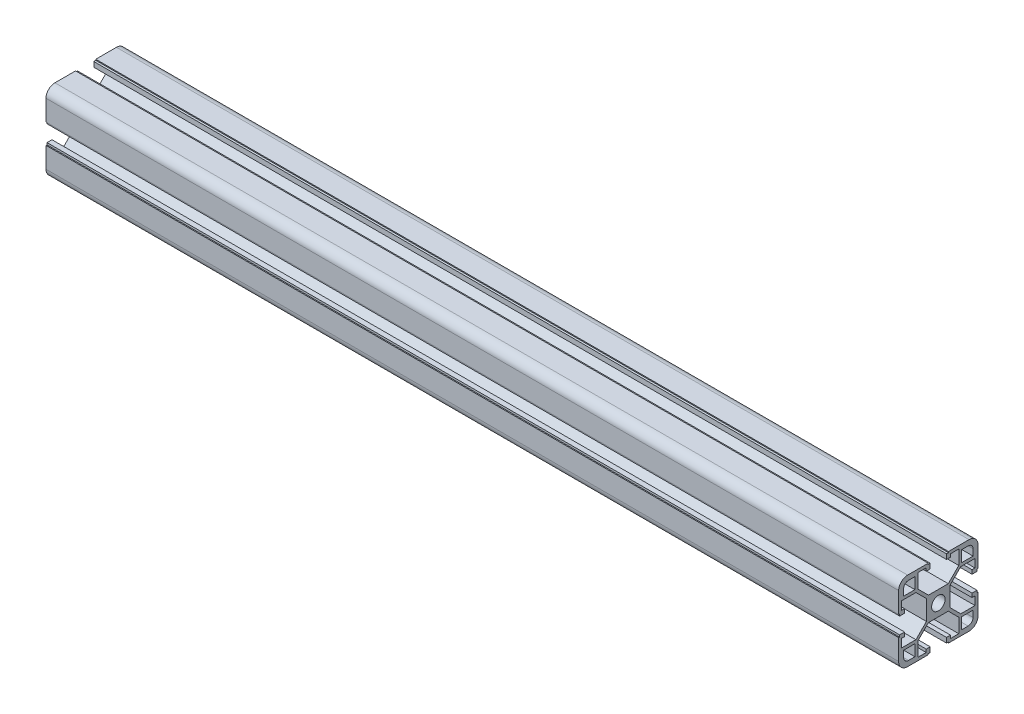
SolidWorks part; units mm, degrees
ref_plane "前视基准面" through (0, 0, 0) normal (0, 0, 1) x (1, 0, 0)
ref_plane "上视基准面" through (0, 0, 0) normal (0, 1, 0) x (1, 0, 0)
ref_plane "右视基准面" through (0, 0, 0) normal (1, 0, 0) x (0, 0, -1)
sketch "草图1" plane through (0, 0, 0) normal (0, 1, 0) x (1, 0, 0)
  line L0 (-165, 0) -> (265, 0)
  line L1 (0, 101.9544) -> (0, -23.3477) construction
  dimension "D1" = 430
  dimension "D2" = 165
other "铝型材 40 X 40L X R4.5(1)"
ref_plane "基准面1" through (-165, 0, 0) normal (1, 0, 0) x (0, 0, -1)
sketch "Sketch1" plane through (-165, 0, 0) normal (1, 0, 0) x (0, 0, -1)
  line L0 (-5.1, 20) -> (-5.1, 19.5)
  line L1 (-5.1, 19.5) -> (-4.1, 19.5)
  line L2 (-4.1, 19.5) -> (-4.1, 17)
  line L3 (-6.1, 18.5) -> (-10.3, 18.5)
  line L4 (-15.5, -20) -> (-5.1, -20)
  line L5 (-20, -15.5) -> (-20, -5.1)
  line L6 (15.5, 20) -> (5.1, 20)
  line L7 (20, 15.5) -> (20, 5.1)
  line L8 (0, 14.8756) -> (0, 0) construction
  line L9 (0, 0) -> (14.1675, 0) construction
  line L10 (-10.3, 18.5) -> (-10.3, 11.3)
  line L11 (-10.3, 11.3) -> (-5, 6)
  line L12 (-5, 6) -> (5, 6)
  line L13 (10.3, 11.3) -> (5, 6)
  line L14 (10.3, 18.5) -> (10.3, 11.3)
  line L15 (6.1, 18.5) -> (10.3, 18.5)
  line L16 (4.1, 19.5) -> (4.1, 17)
  line L17 (5.1, 19.5) -> (4.1, 19.5)
  line L18 (5.1, 20) -> (5.1, 19.5)
  line L19 (-5.1, 20) -> (-15.5, 20)
  line L20 (20, 5.1) -> (19.5, 5.1)
  line L21 (11.8, 17.5) -> (15, 17.5)
  line L22 (11.8, 17.5) -> (11.8, 11.8)
  line L23 (11.8, 11.8) -> (17.5, 11.8)
  line L24 (17.5, 15) -> (17.5, 11.8)
  line L25 (19.5, 5.1) -> (19.5, 4.1)
  line L26 (19.5, 4.1) -> (17, 4.1)
  line L27 (17, 6.1) -> (17, 4.1)
  line L28 (18.5, 6.1) -> (17, 6.1)
  line L29 (18.5, 6.1) -> (18.5, 10.3)
  line L30 (18.5, 10.3) -> (11.3, 10.3)
  line L31 (11.3, 10.3) -> (6, 5)
  line L32 (6, 5) -> (6, -5)
  line L33 (11.3, -10.3) -> (6, -5)
  line L34 (18.5, -10.3) -> (11.3, -10.3)
  line L35 (18.5, -6.1) -> (18.5, -10.3)
  line L36 (18.5, -6.1) -> (17, -6.1)
  line L37 (17, -4.1) -> (17, -6.1)
  line L38 (19.5, -4.1) -> (17, -4.1)
  line L39 (19.5, -5.1) -> (19.5, -4.1)
  line L40 (20, -5.1) -> (19.5, -5.1)
  line L41 (5.1, -20) -> (5.1, -19.5)
  line L42 (5.1, -19.5) -> (4.1, -19.5)
  line L43 (4.1, -19.5) -> (4.1, -17)
  line L44 (6.1, -17) -> (4.1, -17)
  line L45 (6.1, -18.5) -> (6.1, -17)
  line L46 (6.1, -18.5) -> (10.3, -18.5)
  line L47 (10.3, -18.5) -> (10.3, -11.3)
  line L48 (10.3, -11.3) -> (5, -6)
  line L49 (5, -6) -> (-5, -6)
  line L50 (-10.3, -11.3) -> (-5, -6)
  line L51 (-10.3, -18.5) -> (-10.3, -11.3)
  line L52 (-6.1, -18.5) -> (-10.3, -18.5)
  line L53 (-6.1, -18.5) -> (-6.1, -17)
  line L54 (-4.1, -17) -> (-6.1, -17)
  line L55 (-4.1, -19.5) -> (-4.1, -17)
  line L56 (-5.1, -19.5) -> (-4.1, -19.5)
  line L57 (-5.1, -20) -> (-5.1, -19.5)
  line L58 (-20, -5.1) -> (-19.5, -5.1)
  line L59 (5.1, -20) -> (15.5, -20)
  line L60 (-20, 5.1) -> (-20, 15.5)
  line L61 (-19.5, -5.1) -> (-19.5, -4.1)
  line L62 (-6.1, 18.5) -> (-6.1, 17)
  line L63 (-6.1, 17) -> (-4.1, 17)
  line L64 (6.1, 18.5) -> (6.1, 17)
  line L65 (4.1, 17) -> (6.1, 17)
  line L66 (-19.5, -4.1) -> (-17, -4.1)
  line L67 (-15, 17.5) -> (-11.8, 17.5)
  line L68 (-17.5, 15) -> (-17.5, 11.8)
  line L69 (-17.5, 11.8) -> (-11.8, 11.8)
  line L70 (-11.8, 17.5) -> (-11.8, 11.8)
  line L71 (-17, -6.1) -> (-17, -4.1)
  line L72 (-18.5, -6.1) -> (-17, -6.1)
  line L73 (-18.5, -6.1) -> (-18.5, -10.3)
  line L74 (-18.5, -10.3) -> (-11.3, -10.3)
  line L75 (-11.3, -10.3) -> (-6, -5)
  line L76 (-6, -5) -> (-6, 5)
  line L77 (-11.3, 10.3) -> (-6, 5)
  line L78 (-18.5, 10.3) -> (-11.3, 10.3)
  line L79 (-18.5, 6.1) -> (-18.5, 10.3)
  line L80 (-18.5, 6.1) -> (-17, 6.1)
  line L81 (-17, 4.1) -> (-17, 6.1)
  line L82 (-19.5, 4.1) -> (-17, 4.1)
  line L83 (-19.5, 5.1) -> (-19.5, 4.1)
  line L84 (-20, 5.1) -> (-19.5, 5.1)
  line L85 (20, -5.1) -> (20, -15.5)
  line L87 (-17.5, -11.8) -> (-11.8, -11.8)
  line L88 (-17.5, -11.8) -> (-17.5, -15)
  line L89 (-15, -17.5) -> (-11.8, -17.5)
  line L90 (-11.8, -11.8) -> (-11.8, -17.5)
  line L91 (11.8, -11.8) -> (17.5, -11.8)
  line L92 (11.8, -11.8) -> (11.8, -17.5)
  line L93 (11.8, -17.5) -> (15, -17.5)
  line L94 (17.5, -11.8) -> (17.5, -15)
  circle A0 centre (0, 0) radius 3.4
  arc A1 (-20, 15.5) -> (-15.5, 20) centre (-15.5, 15.5) cw
  arc A2 (20, 15.5) -> (15.5, 20) centre (15.5, 15.5) ccw
  arc A3 (-15.5, -20) -> (-20, -15.5) centre (-15.5, -15.5) cw
  arc A4 (15.5, -20) -> (20, -15.5) centre (15.5, -15.5) ccw
  arc A5 (-15, 17.5) -> (-17.5, 15) centre (-15, 15) ccw
  arc A6 (17.5, 15) -> (15, 17.5) centre (15, 15) ccw
  arc A7 (17.5, -15) -> (15, -17.5) centre (15, -15) cw
  arc A8 (-17.5, -15) -> (-15, -17.5) centre (-15, -15) ccw
  point P2 (0, 10)
  point P4 (0, 0)
  point P5 (-20, -20)
  point P6 (20, -20)
  point P7 (20, 20)
  point P8 (-20, 20)
  point P36 (-20, 20)
  point P39 (20, 20)
  point P121 (0, 0)
  dimension "D1" = 20.6
  dimension "D2" = 40
  dimension "D3" = 8.2
  dimension "D4" = 10.2
  dimension "D5" = 14
  dimension "D6" = 6.8
  dimension "D7" = 4.5
  dimension "D8" = 45
  dimension "D12" = 2.5
  dimension "D13" = 5.7
  dimension "D14" = 1.5
  dimension "D18" = 2.5
  dimension "D19" = 2.5
  dimension "D15" = 2.5
  dimension "D9" = 0.5
  dimension "D10" = 1.5
  dimension "D11" = 10
  dimension "D16" = 3
  dimension "D17" = 2
  dimension "D20" = 1.5
  dimension "D21" = 2.5
sketch "草图2" plane through (0, 20, 0) normal (0, 1, 0) x (1, 0, 0)
  line L0 (0, 86.1779) -> (0, -55.3806) construction
  line L2 (-60.2995, 0) -> (128.123, 0) construction
  circle A0 centre (-1, 0) radius 2.5
  circle A1 centre (108, 0) radius 2.5
  dimension "D1" = 5
  dimension "D2" = 1
  dimension "D3" = 5
  dimension "D4" = 109
extrude "切除-拉伸1" cut sketch "草图2" against normal through all
